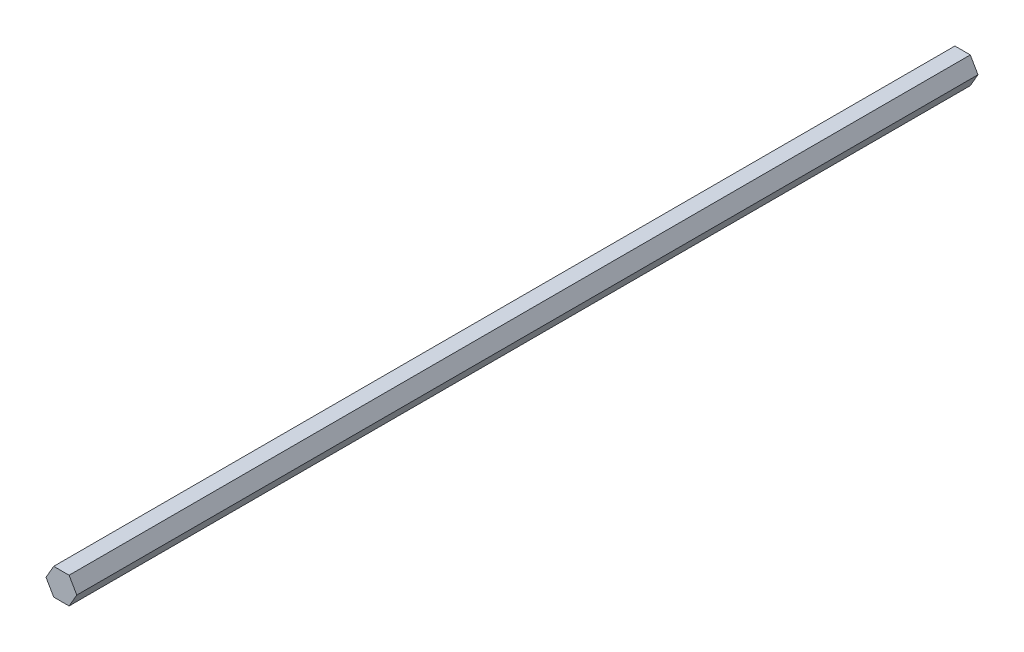
SolidWorks part; units mm, degrees
ref_plane "Front Plane" through (0, 0, 0) normal (0, 0, 1) x (1, 0, 0)
ref_plane "Top Plane" through (0, 0, 0) normal (0, 1, 0) x (1, 0, 0)
ref_plane "Right Plane" through (0, 0, 0) normal (1, 0, 0) x (0, 0, -1)
sketch "Sketch1" plane through (0, 0, 0) normal (0, 0, 1) x (1, 0, 0)
  line L1 (-3.615, 6.2614) -> (-7.23, 0)
  line L2 (-7.23, 0) -> (-3.615, -6.2614)
  line L3 (-3.615, -6.2614) -> (3.615, -6.2614)
  line L4 (3.615, -6.2614) -> (7.23, 0)
  line L5 (7.23, 0) -> (3.615, 6.2614)
  line L6 (3.615, 6.2614) -> (-3.615, 6.2614)
  circle A0 centre (0, 0) radius 6.2614 construction
  point P1 (0, 6.2614)
  dimension "D1" = 7.23
extrude "Boss-Extrude1" add sketch "Sketch1" along normal blind 423.18
